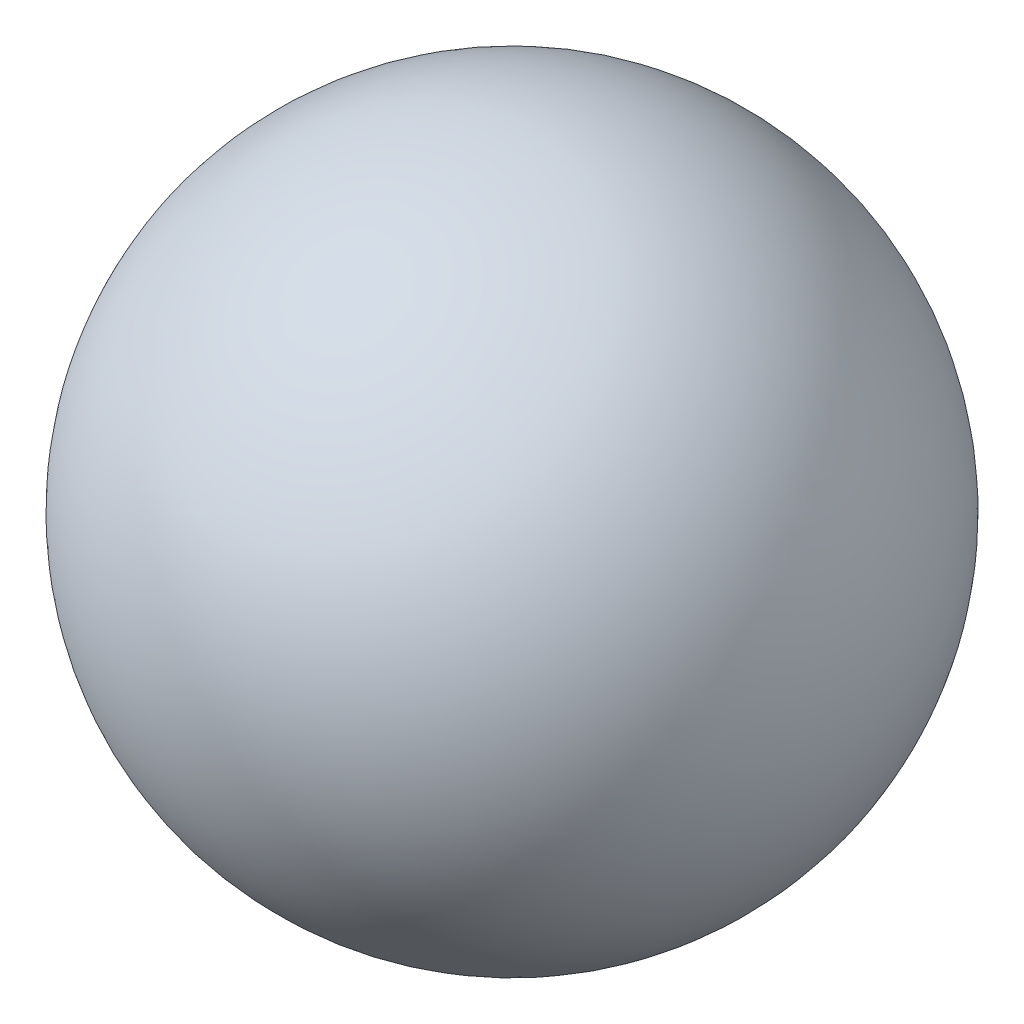
SolidWorks part; units mm, degrees
ref_plane "Front Plane" through (0, 0, 0) normal (0, 0, 1) x (1, 0, 0)
ref_plane "Top Plane" through (0, 0, 0) normal (0, 1, 0) x (1, 0, 0)
ref_plane "Right Plane" through (0, 0, 0) normal (1, 0, 0) x (0, 0, -1)
sketch "Sketch1" plane through (0, 0, 0) normal (0, 1, 0) x (1, 0, 0)
  line L0 (-8.8432, 0) -> (12.856, 0) construction
  line L1 (-6.35, 0) -> (6.35, 0)
  arc A0 (6.35, 0) -> (-6.35, 0) centre (0, 0) ccw
  dimension "D1" = 6.35
revolve "Revolve5" add sketch "Sketch1" angle 360 about L0
